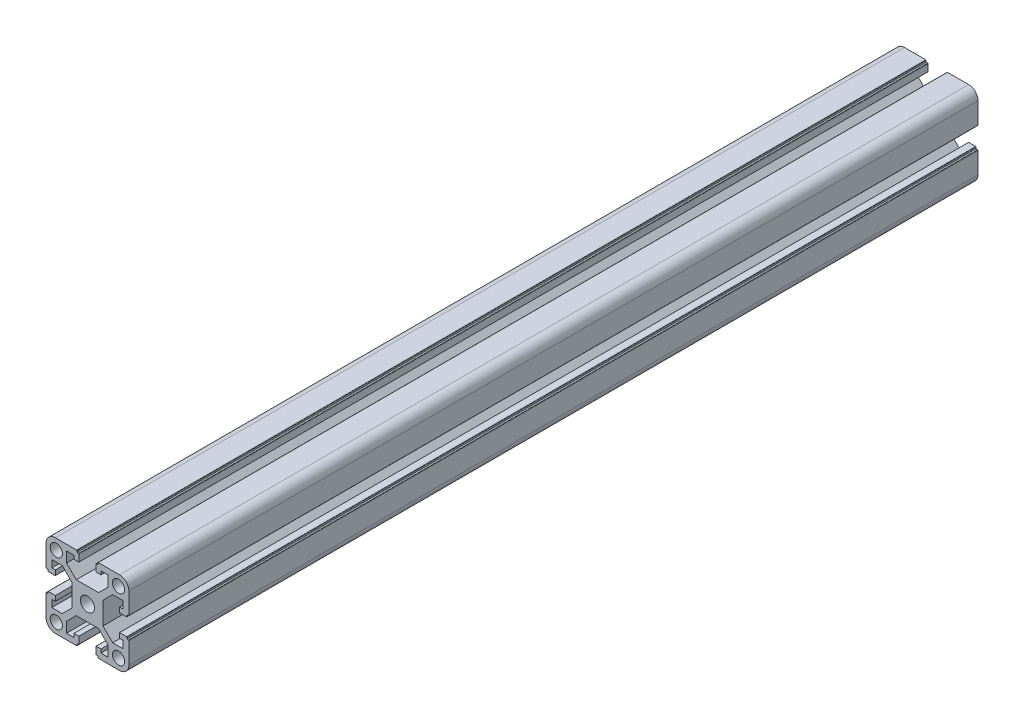
SolidWorks part; units mm, degrees
material "6061-T6 (SS)"
ref_plane "前视基准面" through (0, 0, 0) normal (0, 0, 1) x (1, 0, 0)
ref_plane "上视基准面" through (0, 0, 0) normal (0, 1, 0) x (1, 0, 0)
ref_plane "右视基准面" through (0, 0, 0) normal (1, 0, 0) x (0, 0, -1)
ref_plane "基准面1" through (0, 0, 50) normal (0, 0, 1) x (1, 0, 0)
sketch "草图1" plane through (0, 0, 50) normal (0, 0, 1) x (1, 0, 0)
  line L0 (-1518.245, 3588.0043) -> (-1518.245, 3582.9756)
  line L1 (-1518.245, 3582.9756) -> (-1522.9163, 3578.3043)
  line L2 (-1522.9163, 3578.3043) -> (-1533.6737, 3578.3043)
  line L3 (-1533.6737, 3578.3043) -> (-1538.345, 3582.9756)
  line L4 (-1538.345, 3582.9756) -> (-1538.345, 3588.0043)
  line L5 (-1538.345, 3588.0043) -> (-1534.845, 3588.0043)
  line L6 (-1534.845, 3588.0043) -> (-1534.845, 3586.3043)
  line L7 (-1534.845, 3586.3043) -> (-1532.445, 3586.3043)
  line L8 (-1532.445, 3586.3043) -> (-1532.445, 3589.7043)
  line L9 (-1532.645, 3589.9043) -> (-1533.345, 3589.9043)
  line L10 (-1533.345, 3589.9043) -> (-1533.345, 3590.6043)
  line L11 (-1533.545, 3590.8043) -> (-1543.795, 3590.8043)
  line L12 (-1548.295, 3586.3043) -> (-1548.295, 3576.0543)
  line L13 (-1548.095, 3575.8543) -> (-1547.395, 3575.8543)
  line L14 (-1547.395, 3575.8543) -> (-1547.395, 3575.1543)
  line L15 (-1547.195, 3574.9543) -> (-1543.795, 3574.9543)
  line L16 (-1543.795, 3574.9543) -> (-1543.795, 3577.3543)
  line L17 (-1543.795, 3577.3543) -> (-1545.495, 3577.3543)
  line L18 (-1545.495, 3577.3543) -> (-1545.495, 3580.8543)
  line L19 (-1545.495, 3580.8543) -> (-1540.4663, 3580.8543)
  line L20 (-1540.4663, 3580.8543) -> (-1535.795, 3576.183)
  line L21 (-1535.795, 3576.183) -> (-1535.795, 3565.4256)
  line L22 (-1535.795, 3565.4256) -> (-1540.4663, 3560.7543)
  line L23 (-1540.4663, 3560.7543) -> (-1545.495, 3560.7543)
  line L24 (-1545.495, 3560.7543) -> (-1545.495, 3564.2543)
  line L25 (-1545.495, 3564.2543) -> (-1543.795, 3564.2543)
  line L26 (-1543.795, 3564.2543) -> (-1543.795, 3566.6543)
  line L27 (-1543.795, 3566.6543) -> (-1547.195, 3566.6543)
  line L28 (-1547.395, 3566.4543) -> (-1547.395, 3565.7543)
  line L29 (-1547.395, 3565.7543) -> (-1548.095, 3565.7543)
  line L30 (-1548.295, 3565.5543) -> (-1548.295, 3555.3043)
  line L31 (-1543.795, 3550.8043) -> (-1533.545, 3550.8043)
  line L32 (-1533.345, 3551.0043) -> (-1533.345, 3551.7043)
  line L33 (-1533.345, 3551.7043) -> (-1532.645, 3551.7043)
  line L34 (-1532.445, 3551.9043) -> (-1532.445, 3555.3043)
  line L35 (-1532.445, 3555.3043) -> (-1534.845, 3555.3043)
  line L36 (-1534.845, 3555.3043) -> (-1534.845, 3553.6043)
  line L37 (-1534.845, 3553.6043) -> (-1538.345, 3553.6043)
  line L38 (-1538.345, 3553.6043) -> (-1538.345, 3558.633)
  line L39 (-1538.345, 3558.633) -> (-1533.6737, 3563.3043)
  line L40 (-1533.6737, 3563.3043) -> (-1522.9163, 3563.3043)
  line L41 (-1522.9163, 3563.3043) -> (-1518.245, 3558.633)
  line L42 (-1518.245, 3558.633) -> (-1518.245, 3553.6043)
  line L43 (-1518.245, 3553.6043) -> (-1521.745, 3553.6043)
  line L44 (-1521.745, 3553.6043) -> (-1521.745, 3555.3043)
  line L45 (-1521.745, 3555.3043) -> (-1524.145, 3555.3043)
  line L46 (-1524.145, 3555.3043) -> (-1524.145, 3551.9043)
  line L47 (-1523.945, 3551.7043) -> (-1523.245, 3551.7043)
  line L48 (-1523.245, 3551.7043) -> (-1523.245, 3551.0043)
  line L49 (-1523.045, 3550.8043) -> (-1512.795, 3550.8043)
  line L50 (-1508.295, 3555.3043) -> (-1508.295, 3565.5543)
  line L51 (-1508.495, 3565.7543) -> (-1509.195, 3565.7543)
  line L52 (-1509.195, 3565.7543) -> (-1509.195, 3566.4543)
  line L53 (-1509.395, 3566.6543) -> (-1512.795, 3566.6543)
  line L54 (-1512.795, 3566.6543) -> (-1512.795, 3564.2543)
  line L55 (-1512.795, 3564.2543) -> (-1511.095, 3564.2543)
  line L56 (-1511.095, 3564.2543) -> (-1511.095, 3560.7543)
  line L57 (-1511.095, 3560.7543) -> (-1516.1237, 3560.7543)
  line L58 (-1516.1237, 3560.7543) -> (-1520.795, 3565.4256)
  line L59 (-1520.795, 3565.4256) -> (-1520.795, 3576.183)
  line L60 (-1520.795, 3576.183) -> (-1516.1237, 3580.8543)
  line L61 (-1516.1237, 3580.8543) -> (-1511.095, 3580.8543)
  line L62 (-1511.095, 3580.8543) -> (-1511.095, 3577.3543)
  line L63 (-1511.095, 3577.3543) -> (-1512.795, 3577.3543)
  line L64 (-1512.795, 3577.3543) -> (-1512.795, 3574.9543)
  line L65 (-1512.795, 3574.9543) -> (-1509.395, 3574.9543)
  line L66 (-1509.195, 3575.1543) -> (-1509.195, 3575.8543)
  line L67 (-1509.195, 3575.8543) -> (-1508.495, 3575.8543)
  line L68 (-1508.295, 3576.0543) -> (-1508.295, 3586.3043)
  line L69 (-1512.795, 3590.8043) -> (-1523.045, 3590.8043)
  line L70 (-1523.245, 3590.6043) -> (-1523.245, 3589.9043)
  line L71 (-1523.245, 3589.9043) -> (-1523.945, 3589.9043)
  line L72 (-1524.145, 3589.7043) -> (-1524.145, 3586.3043)
  line L73 (-1524.145, 3586.3043) -> (-1521.745, 3586.3043)
  line L74 (-1521.745, 3586.3043) -> (-1521.745, 3588.0043)
  line L75 (-1521.745, 3588.0043) -> (-1518.245, 3588.0043)
  circle A0 centre (-1513.27, 3555.7793) radius 2.95
  circle A1 centre (-1528.295, 3570.8043) radius 3.4
  circle A2 centre (-1513.27, 3585.8293) radius 2.95
  arc A3 (-1532.445, 3589.7043) -> (-1532.645, 3589.9043) centre (-1532.645, 3589.7043) ccw
  arc A4 (-1533.345, 3590.6043) -> (-1533.545, 3590.8043) centre (-1533.545, 3590.6043) ccw
  arc A5 (-1543.795, 3590.8043) -> (-1548.295, 3586.3043) centre (-1543.795, 3586.3043) ccw
  arc A6 (-1548.295, 3576.0543) -> (-1548.095, 3575.8543) centre (-1548.095, 3576.0543) ccw
  arc A7 (-1547.395, 3575.1543) -> (-1547.195, 3574.9543) centre (-1547.195, 3575.1543) ccw
  arc A8 (-1547.195, 3566.6543) -> (-1547.395, 3566.4543) centre (-1547.195, 3566.4543) ccw
  arc A9 (-1548.095, 3565.7543) -> (-1548.295, 3565.5543) centre (-1548.095, 3565.5543) ccw
  arc A10 (-1548.295, 3555.3043) -> (-1543.795, 3550.8043) centre (-1543.795, 3555.3043) ccw
  arc A11 (-1533.545, 3550.8043) -> (-1533.345, 3551.0043) centre (-1533.545, 3551.0043) ccw
  arc A12 (-1532.645, 3551.7043) -> (-1532.445, 3551.9043) centre (-1532.645, 3551.9043) ccw
  arc A13 (-1524.145, 3551.9043) -> (-1523.945, 3551.7043) centre (-1523.945, 3551.9043) ccw
  arc A14 (-1523.245, 3551.0043) -> (-1523.045, 3550.8043) centre (-1523.045, 3551.0043) ccw
  arc A15 (-1512.795, 3550.8043) -> (-1508.295, 3555.3043) centre (-1512.795, 3555.3043) ccw
  arc A16 (-1508.295, 3565.5543) -> (-1508.495, 3565.7543) centre (-1508.495, 3565.5543) ccw
  arc A17 (-1509.195, 3566.4543) -> (-1509.395, 3566.6543) centre (-1509.395, 3566.4543) ccw
  arc A18 (-1509.395, 3574.9543) -> (-1509.195, 3575.1543) centre (-1509.395, 3575.1543) ccw
  arc A19 (-1508.495, 3575.8543) -> (-1508.295, 3576.0543) centre (-1508.495, 3576.0543) ccw
  arc A20 (-1508.295, 3586.3043) -> (-1512.795, 3590.8043) centre (-1512.795, 3586.3043) ccw
  arc A21 (-1523.045, 3590.8043) -> (-1523.245, 3590.6043) centre (-1523.045, 3590.6043) ccw
  arc A22 (-1523.945, 3589.9043) -> (-1524.145, 3589.7043) centre (-1523.945, 3589.7043) ccw
  circle A23 centre (-1543.32, 3585.8293) radius 2.95
  circle A24 centre (-1543.32, 3555.7793) radius 2.95
extrude "凸台-拉伸1" add sketch "草图1" against normal mid plane 410
ref_plane "基准面2" through (-1528.295, 0, 0) normal (1, 0, 0) x (0, 0, -1)
ref_plane "基准面3" through (0, 3570.8043, 0) normal (0, 1, 0) x (1, 0, 0)
sketch "草图2" plane through (0, 3590.8043, 0) normal (0, 1, 0) x (1, 0, 0)
  line L0 (-1548.295, -50) -> (-1528.295, -50) construction
  line L1 (-1548.295, 155) -> (-1548.295, -255) construction
  line L2 (-1528.295, -5.6375) -> (-1528.295, 5.6375) construction
  line L3 (-1528.295, -50) -> (-1528.295, 135.5309) construction
  circle A0 centre (-1528.295, 65) radius 4
  circle A1 centre (-1528.295, -165) radius 4
  dimension "D1" = 115
  dimension "D2" = 8
extrude "切除-拉伸1" cut sketch "草图2" against normal blind 102
